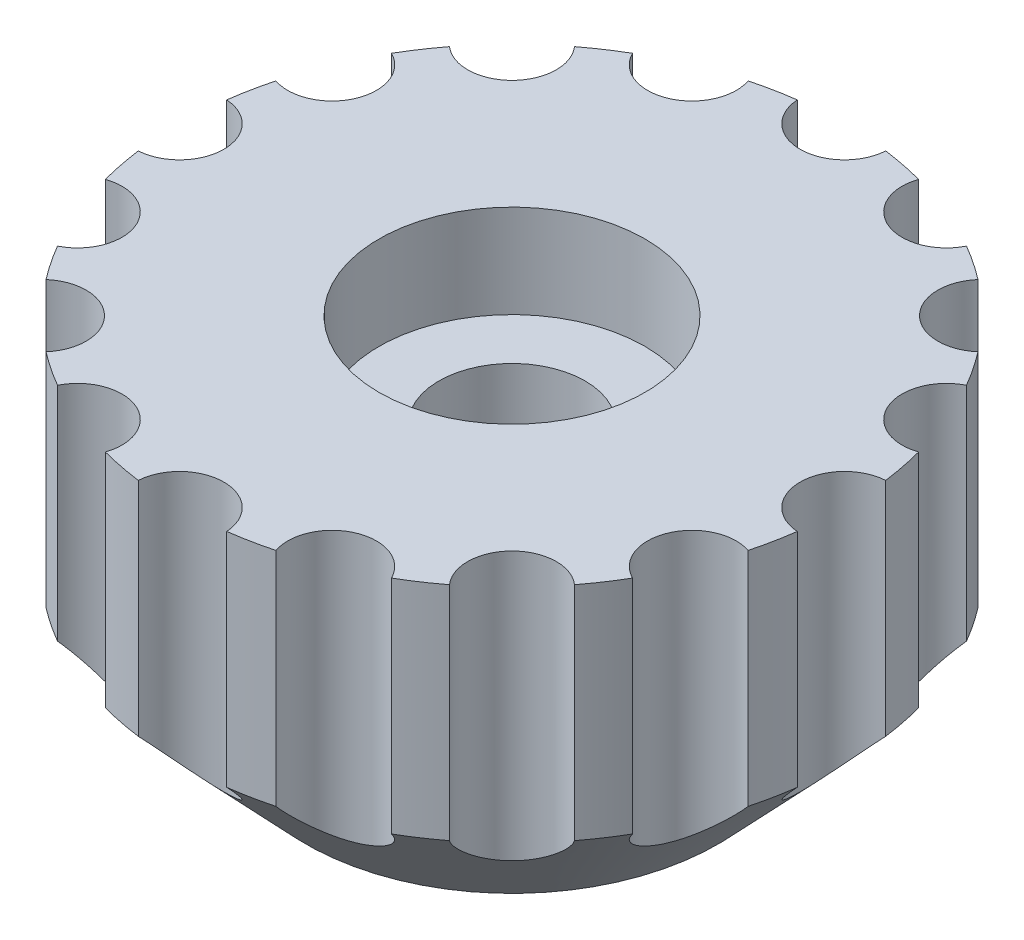
SolidWorks part; units mm, degrees
ref_plane "Plano frontal" through (0, 0, 0) normal (0, 0, 1) x (1, 0, 0)
ref_plane "Plano superior" through (0, 0, 0) normal (0, 1, 0) x (1, 0, 0)
ref_plane "Plano direito" through (0, 0, 0) normal (1, 0, 0) x (0, 0, -1)
sketch "Esboço1" plane through (0, 0, 0) normal (0, 0, 1) x (1, 0, 0)
  line L0 (-3, 8) -> (-7.5, 8)
  line L1 (-7.5, 8) -> (-7.5, 3)
  line L2 (-7.5, 3) -> (-4.65, 0)
  line L3 (-4.65, 0) -> (-1.65, 0)
  line L4 (-3, 8) -> (-3, 5.9)
  line L5 (-3, 5.9) -> (-1.65, 5.9)
  line L6 (-1.65, 0) -> (-1.65, 5.9)
  line L7 (0, 0) -> (0, 13.2193) construction
  dimension "D1" = 3.3
  dimension "D2" = 15
  dimension "D3" = 5
  dimension "D4" = 3
  dimension "D5" = 3
  dimension "D6" = 6
  dimension "D7" = 2.1
revolve "Revolução1" add sketch "Esboço1" angle 360 about L7
sketch "Esboço3" plane through (0, 0, 0) normal (0, -1, 0) x (1, 0, 0)
  line L1 (3.1754, 0) -> (1.5877, 2.75)
  line L2 (1.5877, 2.75) -> (-1.5877, 2.75)
  line L3 (-1.5877, 2.75) -> (-3.1754, 0)
  line L4 (-3.1754, 0) -> (-1.5877, -2.75)
  line L5 (-1.5877, -2.75) -> (1.5877, -2.75)
  line L6 (1.5877, -2.75) -> (3.1754, 0)
  circle A0 centre (0, 0) radius 2.75 construction
  dimension "D1" = 5.5
extrude "Corte-extrusão1" cut sketch "Esboço3" against normal blind 3
sketch "Esboço4" plane through (0, 8, 0) normal (0, 1, 0) x (1, 0, 0)
  circle A0 centre (0, 7.5) radius 1
  circle A1 centre (0, 0) radius 7.5 construction
  circle A2 centre (2.8701, 6.9291) radius 1
  circle A3 centre (5.3033, 5.3033) radius 1
  circle A4 centre (6.9291, 2.8701) radius 1
  circle A5 centre (7.5, 0) radius 1
  circle A6 centre (6.9291, -2.8701) radius 1
  circle A7 centre (5.3033, -5.3033) radius 1
  circle A8 centre (2.8701, -6.9291) radius 1
  circle A9 centre (0, -7.5) radius 1
  circle A10 centre (-2.8701, -6.9291) radius 1
  circle A11 centre (-5.3033, -5.3033) radius 1
  circle A12 centre (-6.9291, -2.8701) radius 1
  circle A13 centre (-7.5, 0) radius 1
  circle A14 centre (-6.9291, 2.8701) radius 1
  circle A15 centre (-5.3033, 5.3033) radius 1
  circle A16 centre (-2.8701, 6.9291) radius 1
  point P36 (0, 0)
  dimension "D1" = 2
  dimension "D2" = 16
extrude "Corte-extrusão2" cut sketch "Esboço4" against normal blind 10
